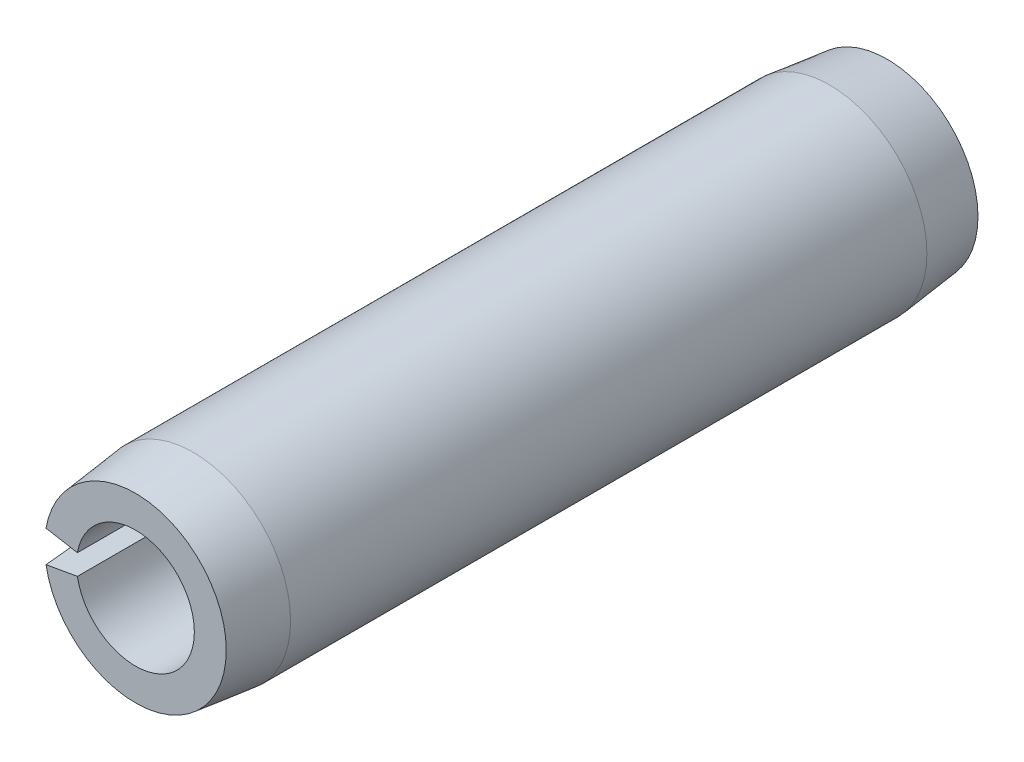
SolidWorks part; units mm, degrees
ref_plane "Front Plane" through (0, 0, 0) normal (0, 0, 1) x (1, 0, 0)
ref_plane "Top Plane" through (0, 0, 0) normal (0, 1, 0) x (1, 0, 0)
ref_plane "Right Plane" through (0, 0, 0) normal (1, 0, 0) x (0, 0, -1)
sketch "Sketch1" plane through (0, 0, 0) normal (0, 0, 1) x (1, 0, 0)
  line L0 (1.2446, 0) -> (2.0574, 0) construction
  line L1 (-2.0261, 0.3573) -> (-1.2257, 0.2161)
  line L2 (-1.2257, -0.2161) -> (-2.0261, -0.3573)
  arc A0 (-2.0261, -0.3573) -> (-2.0261, 0.3573) centre (0, 0) ccw
  arc A1 (-1.2257, -0.2161) -> (-1.2257, 0.2161) centre (0, 0) ccw
  dimension "OD" = 4.1148
  dimension "Wall thickness" = 0.8128
  dimension "D3" = 20
extrude "Extrude1" add sketch "Sketch1" along normal mid plane 15.875
sketch "Sketch2" plane through (0, 0, 0) normal (1, 0, 0) x (0, 0, -1)
  line L0 (0, -2.0574) -> (0, 2.0574) construction
  line L1 (7.9375, 0) -> (-7.9375, 0) construction
  line L2 (7.9375, -1.2446) -> (7.9375, 1.2446) construction
  line L3 (7.9375, 2.0574) -> (-7.9375, 2.0574) construction
  line L4 (7.9375, 2.0574) -> (7.9375, 1.9177)
  line L5 (7.9375, 1.9177) -> (6.7183, 2.0574)
  line L6 (6.7183, 2.0574) -> (7.9375, 2.0574)
  line L7 (7.9375, -2.0574) -> (7.9375, 2.0574) construction
  line L8 (-6.7183, 2.0574) -> (-7.9375, 2.0574)
  line L9 (-7.9375, 1.9177) -> (-6.7183, 2.0574)
  line L10 (-7.9375, 2.0574) -> (-7.9375, 1.9177)
  line L11 (6.7183, -2.0574) -> (7.9375, -2.0574) construction
  line L12 (7.9375, -1.9177) -> (6.7183, -2.0574) construction
  line L13 (7.9375, -2.0574) -> (7.9375, -1.9177) construction
  dimension "B" = 3.8354
  dimension "Chamfer max" = 1.2192
revolve "Cut-Revolve1" cut sketch "Sketch2" angle 360 about L1
sketch "Sketch3" plane through (0, 0, 0) normal (0, 0, 1) x (1, 0, 0)
  line L0 (1.2446, 0) -> (2.0574, 0) construction
  line L1 (1.2446, 0) -> (2.0574, 0)
  circle A0 centre (0, 0) radius 2.0574
  circle A1 centre (0, 0) radius 1.2446
  arc A2 (-2.0261, -0.3573) -> (-2.0261, 0.3573) centre (0, 0) ccw construction
  arc A3 (-1.2257, -0.2161) -> (-1.2257, 0.2161) centre (0, 0) ccw construction
